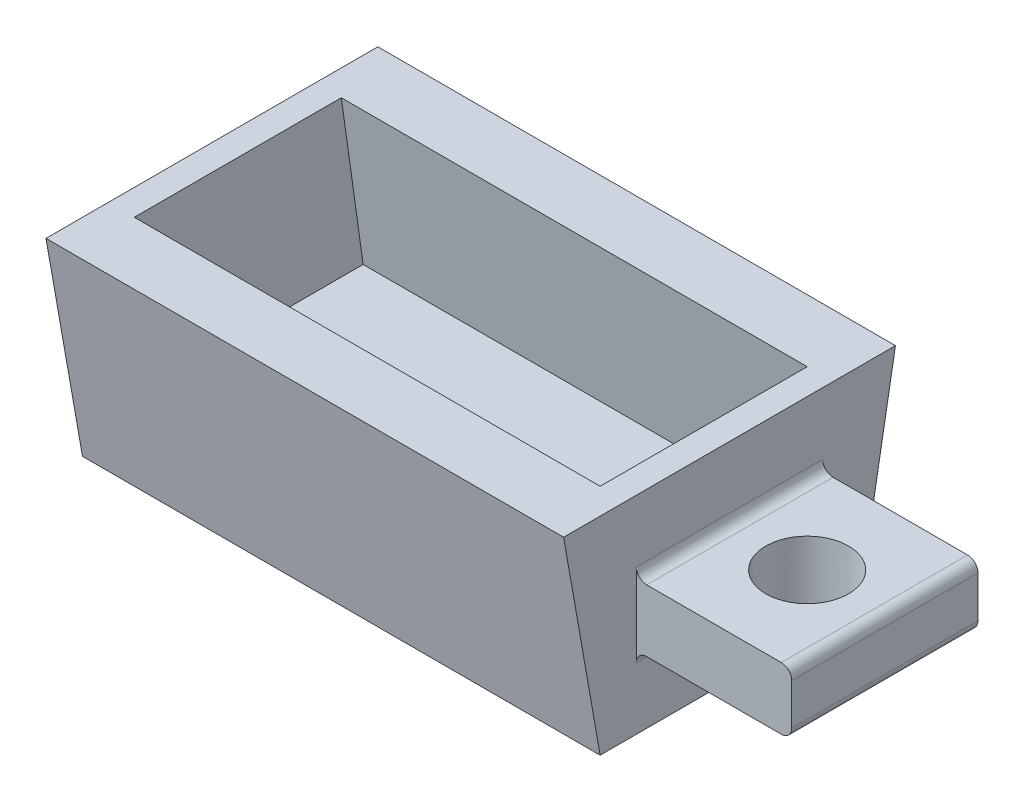
SolidWorks part; units mm, degrees
ref_plane "Front Plane" through (0, 0, 0) normal (0, 0, 1) x (1, 0, 0)
ref_plane "Top Plane" through (0, 0, 0) normal (0, 1, 0) x (1, 0, 0)
ref_plane "Right Plane" through (0, 0, 0) normal (1, 0, 0) x (0, 0, -1)
sketch "Sketch1" plane through (0, 0, 0) normal (0, 1, 0) x (1, 0, 0)
  line L1 (-50, 25) -> (50, 25)
  line L2 (-50, 25) -> (-50, -25)
  line L3 (-50, -25) -> (50, -25)
  line L4 (50, 25) -> (50, -25)
  line L5 (-50, 25) -> (50, -25) construction
  line L6 (-50, -25) -> (50, 25) construction
  point P0 (0, 0)
  dimension "D1" = 50
  dimension "D2" = 100
extrude "Boss-Extrude1" add sketch "Sketch1" along normal blind 40
sketch "Sketch2" plane through (0, 40, 0) normal (0, 1, 0) x (1, 0, 0)
  line L1 (-45, 20) -> (45, 20)
  line L2 (-45, 20) -> (-45, -20)
  line L3 (-45, -20) -> (45, -20)
  line L4 (45, 20) -> (45, -20)
  line L5 (-45, 20) -> (45, -20) construction
  line L6 (-45, -20) -> (45, 20) construction
  point P0 (0, 0)
  dimension "D1" = 40
  dimension "D2" = 90
extrude "Cut-Extrude1" cut sketch "Sketch2" against normal blind 30
sketch "Sketch3" plane through (50, 0, 0) normal (1, 0, 0) x (0, 0, -1)
  line L0 (0, -4.0515) -> (0, 39.4526) construction
  line L1 (-30.1691, 20) -> (31.6823, 20) construction
  line L3 (-25, 0) -> (25, 0) construction
  line L5 (-18, 26) -> (18, 26)
  line L6 (-18, 26) -> (-18, 14)
  line L7 (-18, 14) -> (18, 14)
  line L8 (18, 26) -> (18, 14)
  line L9 (-18, 26) -> (18, 14) construction
  line L10 (-18, 14) -> (18, 26) construction
  point P5 (0, 20)
  dimension "D1" = 20
  dimension "D2" = 12
  dimension "D3" = 36
extrude "Boss-Extrude2" add sketch "Sketch3" along normal blind 30
fillet "Fillet1" radius 2 4 edges at (50, 14, 0) (50, 26, 0) (80, 14, 0) (80, 26, 0)
draft "Draft2" type of draft neutral plane draft angle 10 faces to draft 2 face at (0, 20, -25) face at (0, 20, 25) neutral plane through (0, 0, 0) neutral plane normal (0, -1, 0) parameters "D1"=10
draft "Draft5" type of draft neutral plane draft angle 8 faces to draft 2 face at (0, 25, 20) face at (0, 25, -20) neutral plane through (0, 40, 0) neutral plane normal (0, 1, 0) reverse direction yes parameters "D1"=8
sketch "Sketch4" plane through (0, 26, 0) normal (0, 1, 0) x (1, 0, 0)
  line L1 (93.0318, 0) -> (51.1607, 0) construction
  line L2 (78, -18) -> (52, -18) construction
  line L3 (65, -20.1144) -> (65, 19.8335) construction
  line L4 (78, -18) -> (78, 18) construction
  circle A0 centre (65, 0) radius 8
  dimension "D1" = 18
  dimension "D2" = 13
extrude "Cut-Extrude2" cut sketch "Sketch4" against normal through all draft 3
